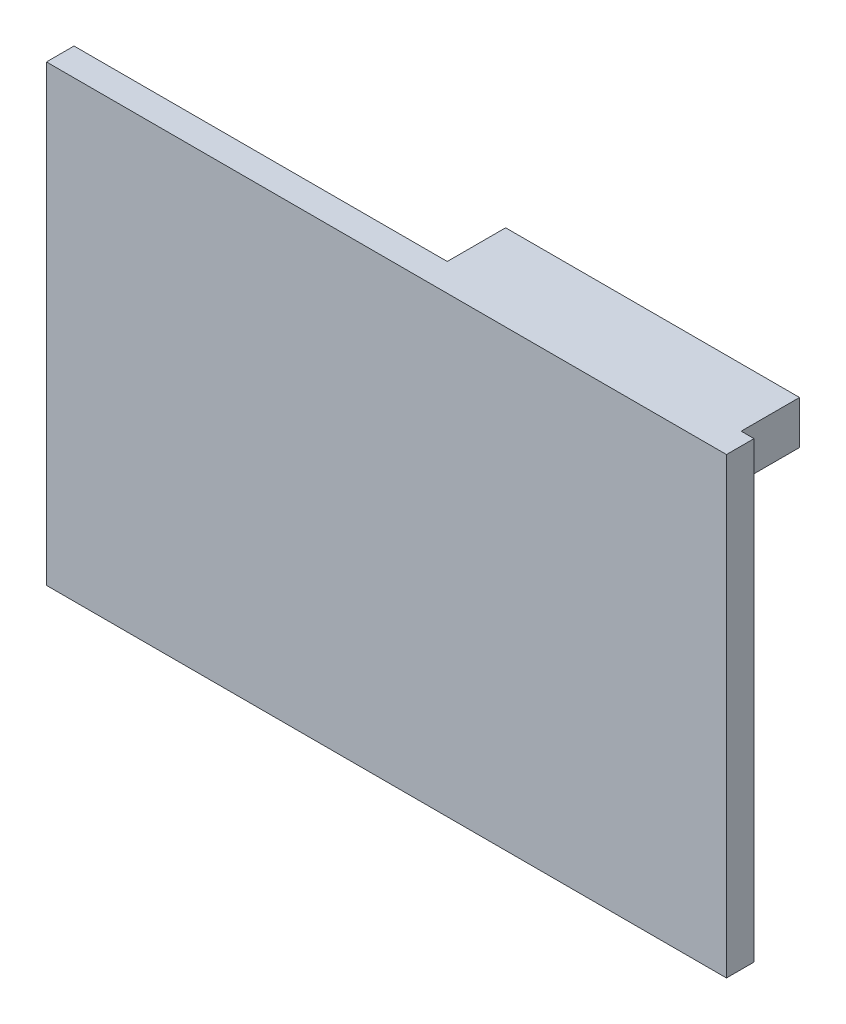
SolidWorks part; units mm, degrees
material "Custom Plastic"
ref_plane "Front Plane" through (0, 0, 0) normal (0, 0, 1) x (1, 0, 0)
ref_plane "Top Plane" through (0, 0, 0) normal (0, 1, 0) x (1, 0, 0)
ref_plane "Right Plane" through (0, 0, 0) normal (1, 0, 0) x (0, 0, -1)
sketch "Sketch1" plane through (0, 0, 0) normal (0, 0, 1) x (1, 0, 0)
  line L1 (-36.9846, 24.6564) -> (36.9846, 24.6564)
  line L2 (-36.9846, 24.6564) -> (-36.9846, -24.6564)
  line L3 (-36.9846, -24.6564) -> (36.9846, -24.6564)
  line L4 (36.9846, 24.6564) -> (36.9846, -24.6564)
  line L5 (-36.9846, 24.6564) -> (36.9846, -24.6564) construction
  line L6 (-36.9846, -24.6564) -> (36.9846, 24.6564) construction
  point P0 (0, 0)
  dimension "D1" = 88.9
  dimension "D2" = 49.3128
extrude "Boss-Extrude1" add sketch "Sketch1" along normal blind 3
sketch "Sketch2" plane through (0, 0, 0) normal (0, 0, 1) x (1, 0, 0)
  line L0 (36.9846, 24.6564) -> (-36.9846, 24.6564) construction
  line L1 (3.6126, 24.6564) -> (35.5844, 24.6564)
  line L2 (3.6126, 24.6564) -> (3.6126, 19.9412)
  line L3 (3.6126, 19.9412) -> (35.5844, 19.9412)
  line L4 (35.5844, 24.6564) -> (35.5844, 19.9412)
  line L5 (-36.9846, 24.6564) -> (-36.9846, -24.6564) construction
  dimension "D1" = 40.5973
  dimension "D2" = 4.7153
  dimension "D3" = 31.9718
extrude "Boss-Extrude2" add sketch "Sketch2" against normal blind 6.35
